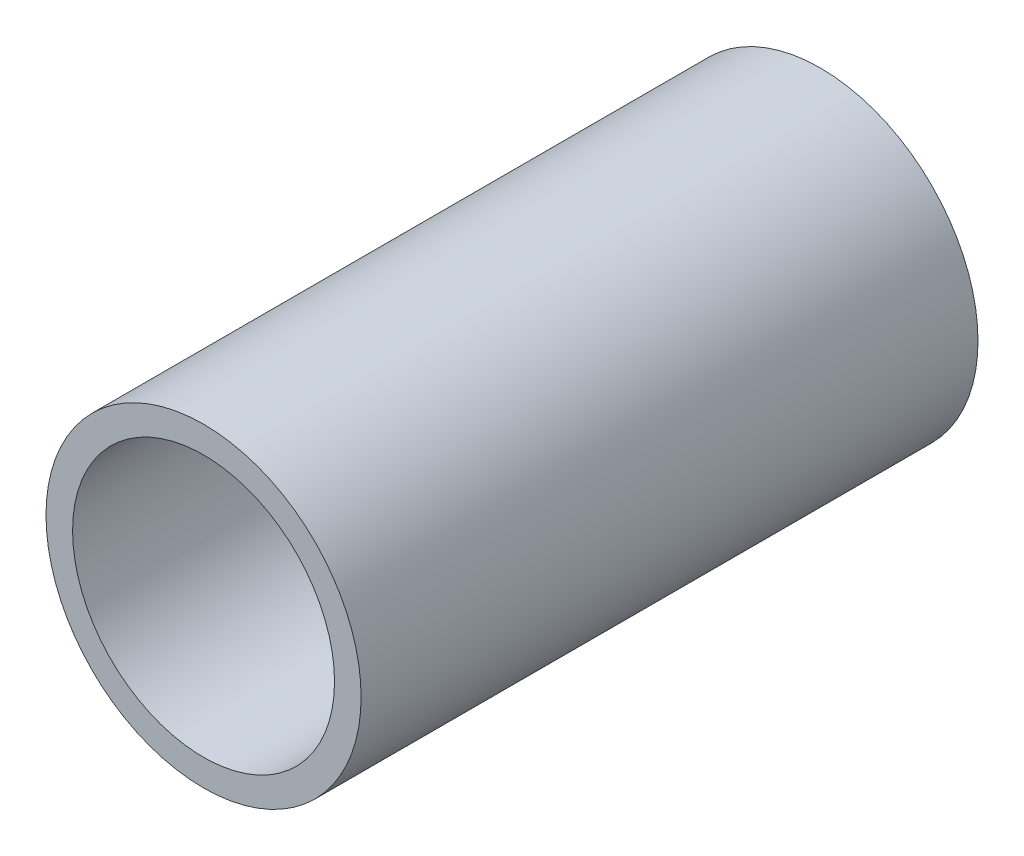
SolidWorks part; units mm, degrees
ref_plane "Front Plane" through (0, 0, 0) normal (0, 0, 1) x (1, 0, 0)
ref_plane "Top Plane" through (0, 0, 0) normal (0, 1, 0) x (1, 0, 0)
ref_plane "Right Plane" through (0, 0, 0) normal (1, 0, 0) x (0, 0, -1)
sketch "Sketch1" plane through (0, 0, 0) normal (0, 0, 1) x (1, 0, 0)
  circle A0 centre (0, 0) radius 21.082
  dimension "Pipe OD" = 42.164
extrude "Extrude-Thin1" add sketch "Sketch1" along normal mid plane 82.55 thin thin type one direction reverse wall 3.556
